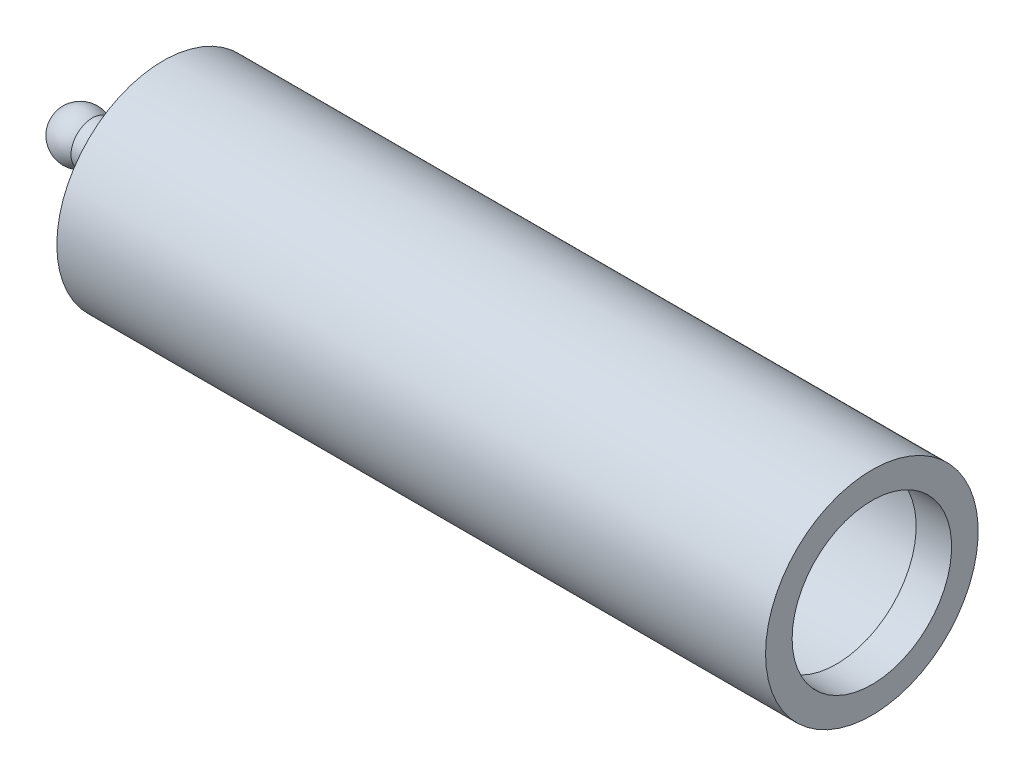
SolidWorks part; units mm, degrees
ref_plane "Front Plane" through (0, 0, 0) normal (0, 0, 1) x (1, 0, 0)
ref_plane "Top Plane" through (0, 0, 0) normal (0, 1, 0) x (1, 0, 0)
ref_plane "Right Plane" through (0, 0, 0) normal (1, 0, 0) x (0, 0, -1)
sketch "Sketch1" plane through (0, 0, 0) normal (0, 0, 1) x (1, 0, 0)
  line L2 (220, 45) -> (220, 60)
  line L3 (220, 60) -> (-180, 60)
  line L4 (-180, 60) -> (-180, 12)
  line L5 (-180, 12) -> (-220, 12)
  line L6 (-220, 12) -> (-220, 0)
  line L7 (-220, 0) -> (-160, 0)
  line L8 (-160, 0) -> (-160, 55)
  line L9 (-160, 55) -> (200, 55)
  line L10 (200, 55) -> (200, 45)
  line L11 (200, 45) -> (220, 45)
  line L12 (-220, 0) -> (220, 0) construction
  line L13 (220, 0) -> (220, 45) construction
  point P3 (210, 45)
  point P8 (0, 0)
  dimension "D3" = 15
  dimension "D2" = 12
  dimension "D1" = 60
  dimension "D4" = 400
  dimension "D5" = 40
  dimension "D6" = 5
  dimension "D7" = 20
  dimension "D8" = 20
revolve "Revolve1" add sketch "Sketch1" angle 360 about L7
sketch "Sketch2" plane through (0, 0, 0) normal (0, 0, 1) x (1, 0, 0)
  line L1 (-240.4933, 0) -> (-212.9733, 0)
  arc A2 (-212.9733, 0) -> (-240.4933, 0) centre (-226.7333, 0) ccw
  dimension "D1" = 13.76
revolve "Ball" add sketch "Sketch2" angle 360 about L1
